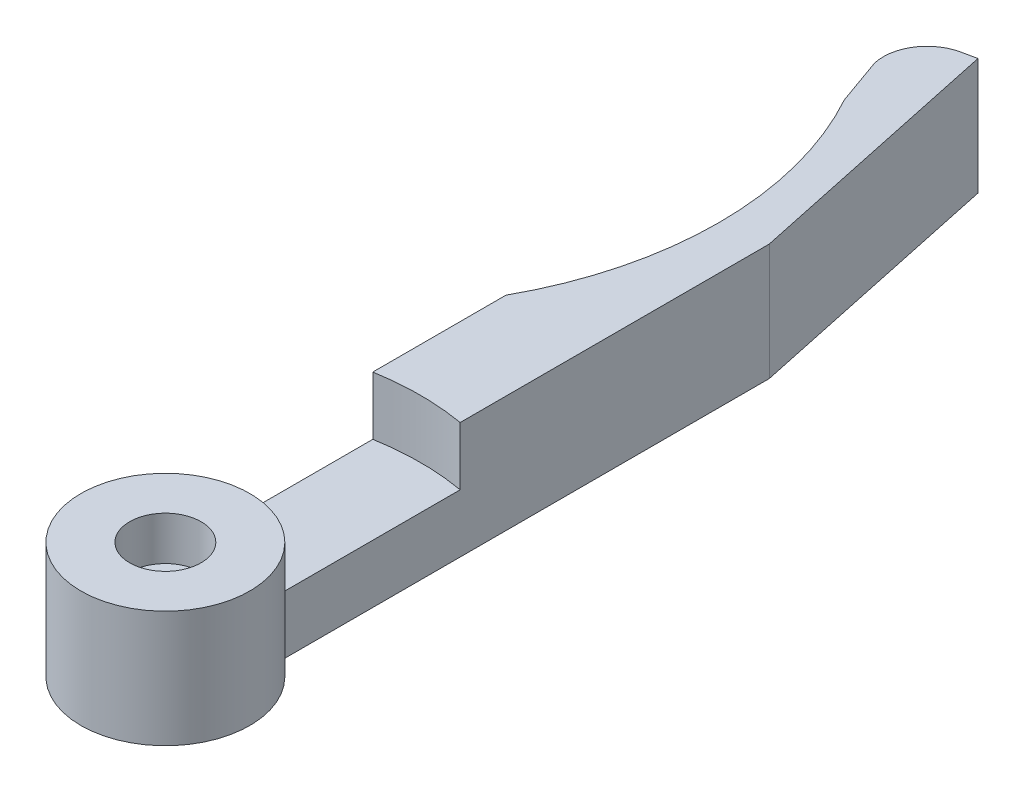
SolidWorks part; units mm, degrees
ref_plane "Plan de face" through (0, 0, 0) normal (0, 0, 1) x (1, 0, 0)
ref_plane "Plan de dessus" through (0, 0, 0) normal (0, 1, 0) x (1, 0, 0)
ref_plane "Plan de droite" through (0, 0, 0) normal (1, 0, 0) x (0, 0, -1)
sketch "Esquisse1" plane through (0, 0, 0) normal (0, 1, 0) x (1, 0, 0)
  line L0 (-3, 50.619) -> (-3, 49.619) construction
  line L1 (2, 55.619) -> (3, 55.619) construction
  line L2 (-3, 55.619) -> (-3, 4.9639) construction
  line L3 (-3, 4.9639) -> (3, 4.9639) construction
  line L4 (3, 55.619) -> (3, 4.9639) construction
  line L5 (-3, 26.381) -> (-3, 4.9639)
  line L7 (-3, 4.9639) -> (3, 4.9639) construction
  line L12 (0, 4.9639) -> (0, -14.5149) construction
  line L13 (-4.1404, 52.822) -> (-3, 49.619)
  line L14 (-1.8453, 56.4495) -> (-0.8672, 56.6574)
  line L15 (-0.8672, 56.6574) -> (3, 38.4639)
  line L16 (3, 38.4639) -> (3, 4.9639)
  arc A0 (-3, 49.619) -> (-3, 26.381) centre (-24, 38) cw
  arc A1 (2, 55.619) -> (-3, 50.619) centre (2, 50.619) ccw construction
  circle A2 centre (0, 0) radius 2.4 construction
  arc A3 (-4.1404, 52.822) -> (-1.8453, 56.4495) centre (-1.2216, 53.5151) cw
  arc A4 (-3, 4.9639) -> (3, 4.9639) centre (0, 0) ccw
  point P19 (0, 38)
  point P25 (-4.3024, 55.9871)
  dimension "D2" = 24
  dimension "D5" = 5
  dimension "D10" = 3
  dimension "D7" = 4.8
  dimension "D11" = 5.8
  dimension "D1" = 6
  dimension "D3" = 21
  dimension "D4" = 6
  dimension "D6" = 38
  dimension "D8" = 3.5
  dimension "D9" = 6.5
  dimension "D12" = 33.5
  dimension "D13" = 12
  dimension "D14" = 18.6
  dimension "D15" = 3.4
  dimension "D16" = 1
extrude "Boss.-Extru.1" add sketch "Esquisse1" along normal blind 8
sketch "Esquisse2" plane through (0, 8, 0) normal (0, 1, 0) x (1, 0, 0)
  line L0 (0, 38) -> (0, 0) construction
  circle A0 centre (0, 0) radius 2.45
  arc A1 (-3, 26.381) -> (-3, 49.619) centre (-24, 38) ccw construction
  dimension "D2" = 4.9
  dimension "D1" = 38
extrude "Enlèv. mat.-Extru.1" cut sketch "Esquisse2" against normal blind 3
sketch "Esquisse3" plane through (0, 5, 0) normal (0, 1, 0) x (1, 0, 0)
  circle A0 centre (0, 0) radius 1.25
  dimension "D1" = 2.5
extrude "Enlèv. mat.-Extru.2" cut sketch "Esquisse3" against normal up to next
sketch "Esquisse4" plane through (0, 0, 0) normal (0, -1, 0) x (1, 0, 0)
  circle A0 centre (0, 0) radius 3
  dimension "D1" = 6
extrude "Enlèv. mat.-Extru.3" cut sketch "Esquisse4" against normal blind 2
sketch "Esquisse5" plane through (0, 8, 0) normal (0, 1, 0) x (1, 0, 0)
  line L0 (-3, 4.9639) -> (-3, 17.2409)
  line L1 (3, 4.9639) -> (3, 17.2409)
  line L2 (3, 4.9639) -> (3, 38.4639) construction
  circle A0 centre (0, 0) radius 5.8 construction
  circle A1 centre (0, 0) radius 17.5 construction
  arc A2 (-3, 4.9639) -> (3, 4.9639) centre (0, 0) ccw construction
  arc A3 (-3, 4.9639) -> (3, 4.9639) centre (0, 0) cw
  arc A4 (-3, 17.2409) -> (3, 17.2409) centre (0, 0) cw
  dimension "D1" = 35
extrude "Enlèv. mat.-Extru.4" cut sketch "Esquisse5" against normal blind 4
